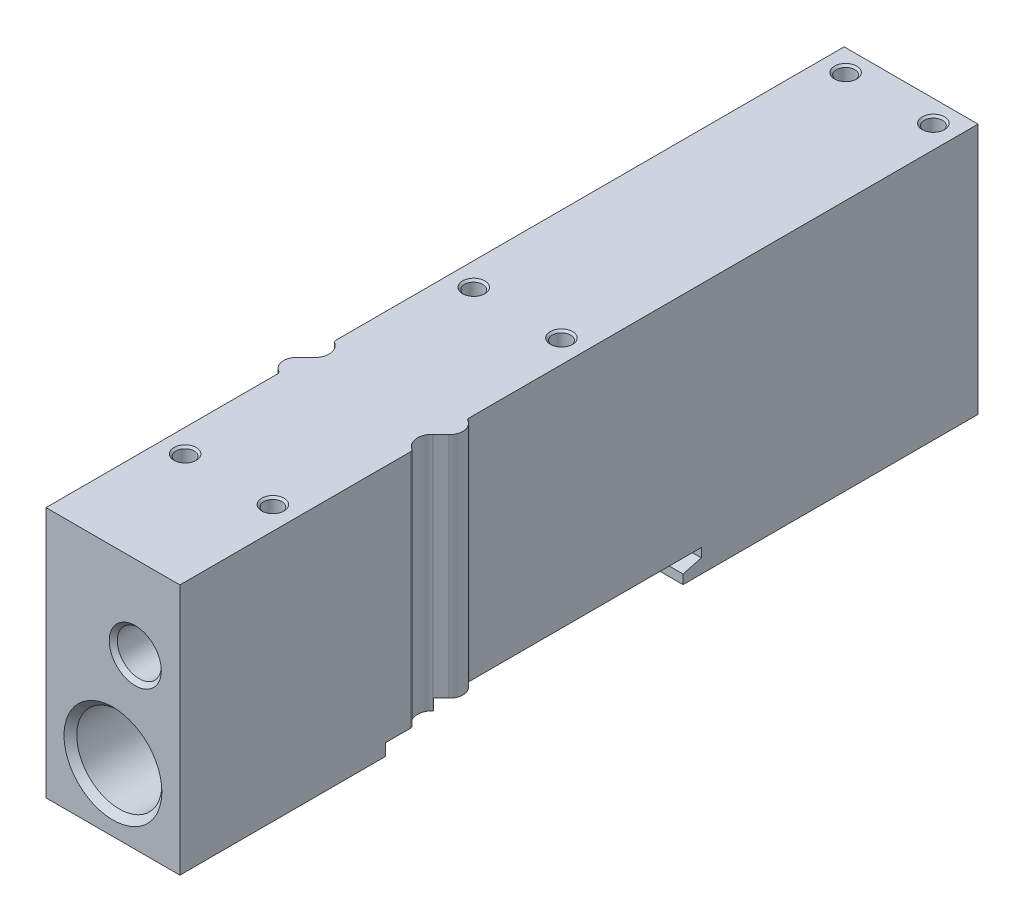
SolidWorks part; units mm, degrees
ref_plane "Front Plane" through (0, 0, 0) normal (0, 0, 1) x (1, 0, 0)
ref_plane "Top Plane" through (0, 0, 0) normal (0, 1, 0) x (1, 0, 0)
ref_plane "Right Plane" through (0, 0, 0) normal (1, 0, 0) x (0, 0, -1)
ref_plane "Plane1" through (0, 1.3, 0) normal (0, 1, 0) x (1, 0, 0)
sketch "Sketch1" plane through (0, 1.3, 0) normal (0, 1, 0) x (1, 0, 0)
  line L0 (0, -22.5419) -> (0, -53.65)
  line L1 (0, -53.65) -> (18, -53.65)
  line L2 (18, -53.65) -> (18, -22.6542)
  line L3 (17.4839, -19.0892) -> (18.5795, -18.0647)
  line L4 (18, -14.7581) -> (18, 53.65)
  line L5 (18, 53.65) -> (0, 53.65)
  line L6 (0, 53.65) -> (0, -14.6458)
  line L7 (0.5161, -18.2108) -> (-0.5795, -19.2353)
  arc A0 (-0.5795, -19.2353) -> (-0.25, -22.1088) centre (0.65, -20.55) ccw
  arc A1 (-0.25, -22.1088) -> (0, -22.5419) centre (-0.5, -22.5419) cw
  arc A2 (18, -22.6542) -> (17.77, -22.2333) centre (17.5, -22.6542) ccw
  arc A3 (17.77, -22.2333) -> (17.4839, -19.0892) centre (18.85, -20.55) cw
  arc A4 (18.5795, -18.0647) -> (18.25, -15.1912) centre (17.35, -16.75) ccw
  arc A5 (18.25, -15.1912) -> (18, -14.7581) centre (18.5, -14.7581) cw
  arc A6 (0, -14.6458) -> (0.23, -15.0667) centre (0.5, -14.6458) ccw
  arc A7 (0.23, -15.0667) -> (0.5161, -18.2108) centre (-0.85, -16.75) cw
extrude "Boss-Extrude1" add sketch "Sketch1" along normal blind 33.8
ref_plane "Plane2" through (0, 0, 0) normal (1, 0, 0) x (0, 0, -1)
sketch "Sketch2" plane through (0, 0, 0) normal (1, 0, 0) x (0, 0, -1)
  line L0 (-26, 2.9) -> (-26, -8.1744)
  line L1 (-26, -8.1744) -> (14, -7.9637)
  line L2 (14, -7.9637) -> (14, 2.5435)
  line L3 (14, 2.5435) -> (16.45, 3.2)
  line L4 (16.45, 3.2) -> (16.45, 4.4)
  line L5 (16.45, 4.4) -> (-19.05, 4.4)
  line L6 (-19.05, 4.4) -> (-19.05, 2.9)
  line L7 (-19.05, 2.9) -> (-26, 2.9)
extrude "Cut-Extrude1" cut sketch "Sketch2" against normal blind 23 and the other way blind 23
ref_plane "Plane3" through (9, 0, 0) normal (1, 0, 0) x (0, 0, -1)
sketch "Sketch3" plane through (9, 0, 0) normal (1, 0, 0) x (0, 0, -1)
  line L0 (-53.65, 9.8) -> (-53.65, 16.3785)
  line L1 (-53.65, 16.3785) -> (-52.794, 15.5225)
  line L2 (-52.794, 15.5225) -> (-40.65, 15.5225)
  line L3 (-40.65, 15.5225) -> (-40.65, 9.8)
  line L4 (-40.65, 9.8) -> (-53.65, 9.8)
  line L5 (-40.65, 9.8) -> (-53.65, 9.8) construction
revolve "Cut-Revolve1" cut sketch "Sketch3" angle 360 about L5
cosmetic thread "Cosmetic Thread1" parameters "D1"=13, "D2"=13.157
ref_plane "Plane4" through (12, 0, 0) normal (1, 0, 0) x (0, 0, -1)
sketch "Sketch4" plane through (12, 0, 0) normal (1, 0, 0) x (0, 0, -1)
  line L0 (-53.65, 23.86) -> (-53.65, 27.36)
  line L1 (-53.65, 27.36) -> (-53.1085, 26.8185)
  line L2 (-53.1085, 26.8185) -> (-46.65, 26.8185)
  line L3 (-46.65, 26.8185) -> (-46.65, 23.86)
  line L4 (-46.65, 23.86) -> (-53.65, 23.86)
  line L5 (-46.65, 23.86) -> (-53.65, 23.86) construction
revolve "Cut-Revolve2" cut sketch "Sketch4" angle 360 about L5
cosmetic thread "Cosmetic Thread2" parameters "D1"=7, "D2"=7
ref_plane "Plane5" through (3.1, 0, 0) normal (1, 0, 0) x (0, 0, -1)
sketch "Sketch5" plane through (3.1, 0, 0) normal (1, 0, 0) x (0, 0, -1)
  line L0 (-38.05, 35.1) -> (-36.55, 35.1)
  line L1 (-36.55, 35.1) -> (-36.8205, 34.8295)
  line L2 (-36.8205, 34.8295) -> (-36.8205, 30.1)
  line L3 (-36.8205, 30.1) -> (-38.05, 30.1)
  line L4 (-38.05, 30.1) -> (-38.05, 35.1)
  line L5 (-38.05, 30.1) -> (-38.05, 35.1) construction
revolve "Cut-Revolve3" cut sketch "Sketch5" angle 360 about L5
cosmetic thread "Cosmetic Thread3" parameters "D1"=5, "D2"=3
ref_plane "Plane6" through (3.1, 0, 0) normal (1, 0, 0) x (0, 0, -1)
sketch "Sketch6" plane through (3.1, 0, 0) normal (1, 0, 0) x (0, 0, -1)
  line L0 (0.75, 35.1) -> (2.25, 35.1)
  line L1 (2.25, 35.1) -> (1.9795, 34.8295)
  line L2 (1.9795, 34.8295) -> (1.9795, 30.1)
  line L3 (1.9795, 30.1) -> (0.75, 30.1)
  line L4 (0.75, 30.1) -> (0.75, 35.1)
  line L5 (0.75, 30.1) -> (0.75, 35.1) construction
revolve "Cut-Revolve4" cut sketch "Sketch6" angle 360 about L5
cosmetic thread "Cosmetic Thread4" parameters "D1"=5, "D2"=3
ref_plane "Plane7" through (3.1, 0, 0) normal (1, 0, 0) x (0, 0, -1)
sketch "Sketch7" plane through (3.1, 0, 0) normal (1, 0, 0) x (0, 0, -1)
  line L0 (50.75, 35.1) -> (52.25, 35.1)
  line L1 (52.25, 35.1) -> (51.9795, 34.8295)
  line L2 (51.9795, 34.8295) -> (51.9795, 30.1)
  line L3 (51.9795, 30.1) -> (50.75, 30.1)
  line L4 (50.75, 30.1) -> (50.75, 35.1)
  line L5 (50.75, 30.1) -> (50.75, 35.1) construction
revolve "Cut-Revolve5" cut sketch "Sketch7" angle 360 about L5
cosmetic thread "Cosmetic Thread5" parameters "D1"=5, "D2"=3
ref_plane "Plane8" through (14.9, 0, 0) normal (1, 0, 0) x (0, 0, -1)
sketch "Sketch8" plane through (14.9, 0, 0) normal (1, 0, 0) x (0, 0, -1)
  line L0 (-38.05, 35.1) -> (-36.55, 35.1)
  line L1 (-36.55, 35.1) -> (-36.8205, 34.8295)
  line L2 (-36.8205, 34.8295) -> (-36.8205, 30.1)
  line L3 (-36.8205, 30.1) -> (-38.05, 30.1)
  line L4 (-38.05, 30.1) -> (-38.05, 35.1)
  line L5 (-38.05, 30.1) -> (-38.05, 35.1) construction
revolve "Cut-Revolve6" cut sketch "Sketch8" angle 360 about L5
cosmetic thread "Cosmetic Thread6" parameters "D1"=5, "D2"=3
ref_plane "Plane9" through (14.9, 0, 0) normal (1, 0, 0) x (0, 0, -1)
sketch "Sketch9" plane through (14.9, 0, 0) normal (1, 0, 0) x (0, 0, -1)
  line L0 (0.75, 35.1) -> (2.25, 35.1)
  line L1 (2.25, 35.1) -> (1.9795, 34.8295)
  line L2 (1.9795, 34.8295) -> (1.9795, 30.1)
  line L3 (1.9795, 30.1) -> (0.75, 30.1)
  line L4 (0.75, 30.1) -> (0.75, 35.1)
  line L5 (0.75, 30.1) -> (0.75, 35.1) construction
revolve "Cut-Revolve7" cut sketch "Sketch9" angle 360 about L5
cosmetic thread "Cosmetic Thread7" parameters "D1"=5, "D2"=3
ref_plane "Plane10" through (14.9, 0, 0) normal (1, 0, 0) x (0, 0, -1)
sketch "Sketch10" plane through (14.9, 0, 0) normal (1, 0, 0) x (0, 0, -1)
  line L0 (50.75, 35.1) -> (52.25, 35.1)
  line L1 (52.25, 35.1) -> (51.9795, 34.8295)
  line L2 (51.9795, 34.8295) -> (51.9795, 30.1)
  line L3 (51.9795, 30.1) -> (50.75, 30.1)
  line L4 (50.75, 30.1) -> (50.75, 35.1)
  line L5 (50.75, 30.1) -> (50.75, 35.1) construction
revolve "Cut-Revolve8" cut sketch "Sketch10" angle 360 about L5
cosmetic thread "Cosmetic Thread8" parameters "D1"=5, "D2"=3
ref_plane "Plane11" through (0, 13, 0) normal (0, 1, 0) x (1, 0, 0)
sketch "Sketch11" plane through (0, 13, 0) normal (0, 1, 0) x (1, 0, 0)
  line L0 (12.75, 53.65) -> (14.665, 53.65)
  line L1 (14.665, 53.65) -> (14.165, 53.15)
  line L2 (14.165, 53.15) -> (14.165, 44.65)
  line L3 (14.165, 44.65) -> (12.75, 43.833)
  line L4 (12.75, 43.833) -> (12.75, 53.65)
  line L5 (12.75, 43.833) -> (12.75, 53.65) construction
revolve "Cut-Revolve9" cut sketch "Sketch11" angle 360 about L5
ref_plane "Plane12" through (0, 13, 0) normal (0, 1, 0) x (1, 0, 0)
sketch "Sketch12" plane through (0, 13, 0) normal (0, 1, 0) x (1, 0, 0)
  line L0 (5.25, 53.65) -> (7.165, 53.65)
  line L1 (7.165, 53.65) -> (6.665, 53.15)
  line L2 (6.665, 53.15) -> (6.665, 44.65)
  line L3 (6.665, 44.65) -> (5.25, 43.833)
  line L4 (5.25, 43.833) -> (5.25, 53.65)
  line L5 (5.25, 43.833) -> (5.25, 53.65) construction
revolve "Cut-Revolve10" cut sketch "Sketch12" angle 360 about L5
